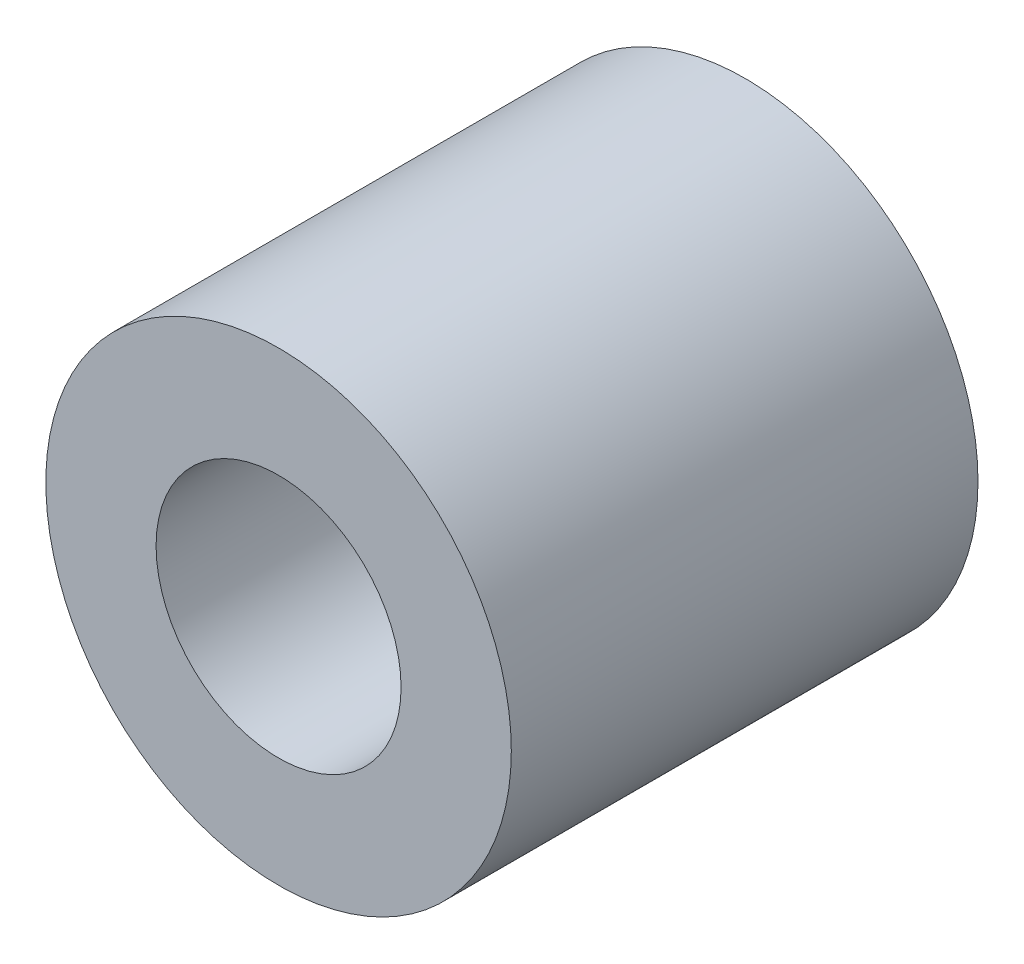
SolidWorks part; units mm, degrees
material "Nylon 6/10"
ref_plane "Front Plane" through (0, 0, 0) normal (0, 0, 1) x (1, 0, 0)
ref_plane "Top Plane" through (0, 0, 0) normal (0, 1, 0) x (1, 0, 0)
ref_plane "Right Plane" through (0, 0, 0) normal (1, 0, 0) x (0, 0, -1)
sketch "Sketch1" plane through (0, 0, 0) normal (0, 1, 0) x (1, 0, 0)
  line L0 (4.75, 4.7625) -> (2.5, 4.7625)
  line L1 (2.5, 4.7625) -> (2.5, -4.7625)
  line L2 (2.5, -4.7625) -> (4.75, -4.7625)
  line L3 (4.75, -4.7625) -> (4.75, 4.7625)
  line L4 (0, 4.7625) -> (0, -4.7625) construction
revolve "Revolve1" add sketch "Sketch1" angle 360 about L4
